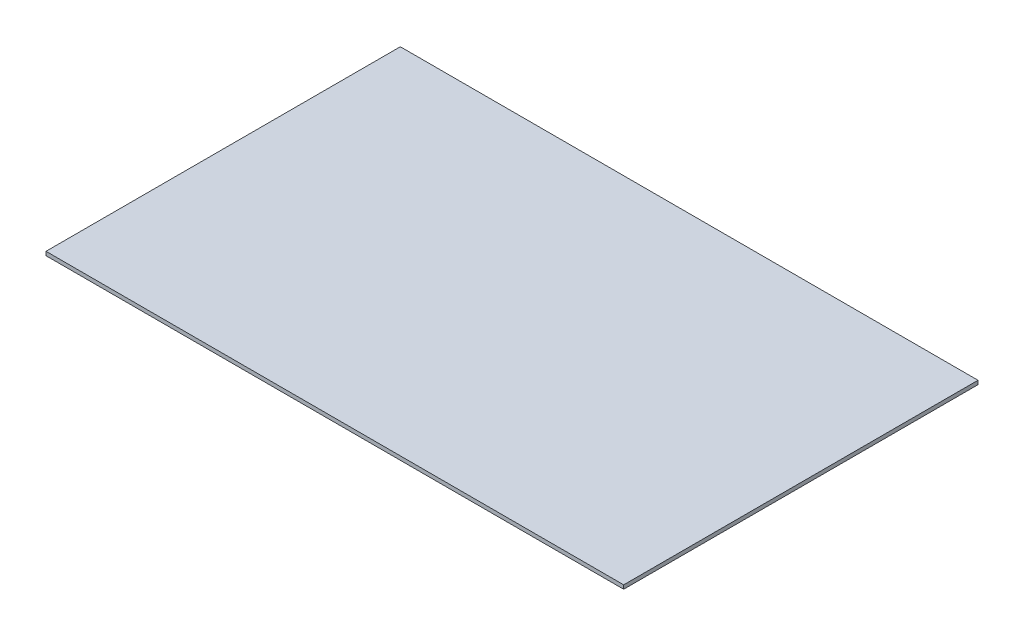
SolidWorks part; units mm, degrees
material "Acrylic (Medium-high impact)"
ref_plane "Front Plane" through (0, 0, 0) normal (0, 0, 1) x (1, 0, 0)
ref_plane "Top Plane" through (0, 0, 0) normal (0, 1, 0) x (1, 0, 0)
ref_plane "Right Plane" through (0, 0, 0) normal (1, 0, 0) x (0, 0, -1)
sketch "Sketch1" plane through (0, 0, 0) normal (0, 1, 0) x (1, 0, 0)
  line L1 (0, 0) -> (-750, 0)
  line L2 (0, 0) -> (0, 460)
  line L3 (0, 460) -> (-750, 460)
  line L4 (-750, 0) -> (-750, 460)
  line L5 (0, 0) -> (-750, 460) construction
  line L6 (0, 460) -> (-750, 0) construction
  point P4 (-375, 230)
  dimension "D1" = 750
  dimension "D2" = 460
extrude "Boss-Extrude1" add sketch "Sketch1" along normal blind 5
